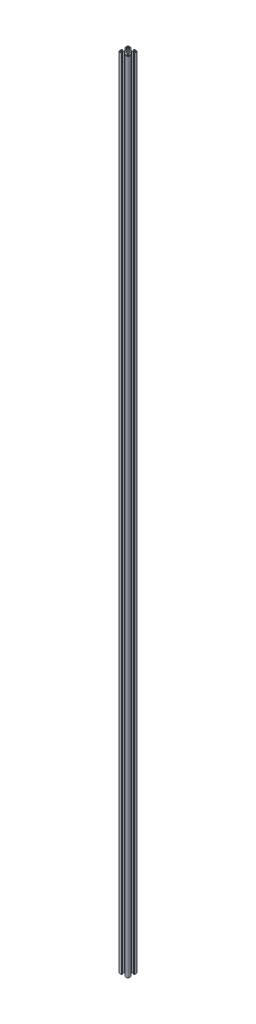
SolidWorks part; units mm, degrees
material "6063-T5"
ref_plane "前视基准面" through (0, 0, 0) normal (0, 0, 1) x (1, 0, 0)
ref_plane "上视基准面" through (0, 0, 0) normal (0, 1, 0) x (1, 0, 0)
ref_plane "右视基准面" through (0, 0, 0) normal (1, 0, 0) x (0, 0, -1)
sketch "草图3" plane through (0, 0, 0) normal (0, 1, 0) x (1, 0, 0)
  line L0 (0, 0) -> (-15, -15) construction
  line L1 (-15, -15) -> (-15, 0) construction
  line L2 (-15, 0) -> (0, 0) construction
  line L3 (-15, -12.5) -> (-15, -5.4)
  line L4 (-14.8, -5.2) -> (-14.4, -5.2)
  line L5 (-14.2, -5) -> (-14.2, -4.3)
  line L6 (-14, -4.1) -> (-13.2, -4.1)
  line L7 (-13.2, -4.1) -> (-13.2, -8.25)
  line L8 (-13.2, -8.25) -> (-9.5228, -8.25)
  line L9 (-9.5228, -8.25) -> (-5.8, -4.5272)
  line L10 (-5.8, -4.5272) -> (-5.8, 4.5272)
  line L11 (-13.2, -12.2) -> (-13.2, -11.05)
  line L12 (-12.2, -10.05) -> (-11.05, -10.05)
  line L13 (-4.5272, -5.8) -> (4.5272, -5.8)
  line L14 (-8.25, -9.5228) -> (-4.5272, -5.8)
  line L15 (-12.2, -13.2) -> (-11.05, -13.2)
  line L16 (-10.05, -12.2) -> (-10.05, -11.05)
  line L17 (-5.2, -14.8) -> (-5.2, -14.4)
  line L18 (-5, -14.2) -> (-4.3, -14.2)
  line L19 (-4.1, -14) -> (-4.1, -13.2)
  line L20 (-4.1, -13.2) -> (-8.25, -13.2)
  line L21 (-8.25, -13.2) -> (-8.25, -9.5228)
  line L22 (-12.5, -15) -> (-5.4, -15)
  line L23 (-12.5, 15) -> (-5.4, 15)
  line L24 (-8.25, 13.2) -> (-8.25, 9.5228)
  line L25 (-4.1, 13.2) -> (-8.25, 13.2)
  line L26 (-4.1, 14) -> (-4.1, 13.2)
  line L27 (-5, 14.2) -> (-4.3, 14.2)
  line L28 (-5.2, 14.8) -> (-5.2, 14.4)
  line L29 (-10.05, 12.2) -> (-10.05, 11.05)
  line L30 (-12.2, 13.2) -> (-11.05, 13.2)
  line L31 (-8.25, 9.5228) -> (-4.5272, 5.8)
  line L32 (-4.5272, 5.8) -> (4.5272, 5.8)
  line L33 (-12.2, 10.05) -> (-11.05, 10.05)
  line L34 (-13.2, 12.2) -> (-13.2, 11.05)
  line L35 (-9.5228, 8.25) -> (-5.8, 4.5272)
  line L36 (-13.2, 8.25) -> (-9.5228, 8.25)
  line L37 (-13.2, 4.1) -> (-13.2, 8.25)
  line L38 (-14, 4.1) -> (-13.2, 4.1)
  line L39 (-14.2, 5) -> (-14.2, 4.3)
  line L40 (-14.8, 5.2) -> (-14.4, 5.2)
  line L41 (-15, 12.5) -> (-15, 5.4)
  line L42 (0, 0) -> (0, -12.3268) construction
  line L43 (15, 12.5) -> (15, 5.4)
  line L44 (14.8, 5.2) -> (14.4, 5.2)
  line L45 (14.2, 5) -> (14.2, 4.3)
  line L46 (14, 4.1) -> (13.2, 4.1)
  line L47 (13.2, 4.1) -> (13.2, 8.25)
  line L48 (13.2, 8.25) -> (9.5228, 8.25)
  line L49 (9.5228, 8.25) -> (5.8, 4.5272)
  line L50 (13.2, 12.2) -> (13.2, 11.05)
  line L51 (12.2, 10.05) -> (11.05, 10.05)
  line L52 (8.25, 9.5228) -> (4.5272, 5.8)
  line L53 (12.2, 13.2) -> (11.05, 13.2)
  line L54 (10.05, 12.2) -> (10.05, 11.05)
  line L55 (5.2, 14.8) -> (5.2, 14.4)
  line L56 (5, 14.2) -> (4.3, 14.2)
  line L57 (4.1, 14) -> (4.1, 13.2)
  line L58 (4.1, 13.2) -> (8.25, 13.2)
  line L59 (8.25, 13.2) -> (8.25, 9.5228)
  line L60 (12.5, 15) -> (5.4, 15)
  line L61 (12.5, -15) -> (5.4, -15)
  line L62 (8.25, -13.2) -> (8.25, -9.5228)
  line L63 (4.1, -13.2) -> (8.25, -13.2)
  line L64 (4.1, -14) -> (4.1, -13.2)
  line L65 (5, -14.2) -> (4.3, -14.2)
  line L66 (5.2, -14.8) -> (5.2, -14.4)
  line L67 (10.05, -12.2) -> (10.05, -11.05)
  line L68 (12.2, -13.2) -> (11.05, -13.2)
  line L69 (8.25, -9.5228) -> (4.5272, -5.8)
  line L70 (12.2, -10.05) -> (11.05, -10.05)
  line L71 (13.2, -12.2) -> (13.2, -11.05)
  line L72 (5.8, -4.5272) -> (5.8, 4.5272)
  line L73 (9.5228, -8.25) -> (5.8, -4.5272)
  line L74 (13.2, -8.25) -> (9.5228, -8.25)
  line L75 (13.2, -4.1) -> (13.2, -8.25)
  line L76 (14, -4.1) -> (13.2, -4.1)
  line L77 (14.2, -5) -> (14.2, -4.3)
  line L78 (14.8, -5.2) -> (14.4, -5.2)
  line L79 (15, -12.5) -> (15, -5.4)
  circle A0 centre (0, 0) radius 3.4
  arc A1 (-12.5, 15) -> (-15, 12.5) centre (-12.5, 12.5) ccw
  arc A2 (15, 12.5) -> (12.5, 15) centre (12.5, 12.5) ccw
  arc A3 (12.5, -15) -> (15, -12.5) centre (12.5, -12.5) ccw
  arc A4 (-15, -12.5) -> (-12.5, -15) centre (-12.5, -12.5) ccw
  arc A5 (-12.2, 13.2) -> (-13.2, 12.2) centre (-12.2, 12.2) ccw
  arc A6 (-12.2, 10.05) -> (-13.2, 11.05) centre (-12.2, 11.05) cw
  arc A7 (-10.05, 11.05) -> (-11.05, 10.05) centre (-11.05, 11.05) cw
  arc A8 (-10.05, 12.2) -> (-11.05, 13.2) centre (-11.05, 12.2) ccw
  arc A9 (11.05, 10.05) -> (10.05, 11.05) centre (11.05, 11.05) cw
  arc A10 (11.05, 13.2) -> (10.05, 12.2) centre (11.05, 12.2) ccw
  arc A11 (13.2, 12.2) -> (12.2, 13.2) centre (12.2, 12.2) ccw
  arc A12 (13.2, 11.05) -> (12.2, 10.05) centre (12.2, 11.05) cw
  arc A13 (12.2, -10.05) -> (13.2, -11.05) centre (12.2, -11.05) cw
  arc A14 (10.05, -11.05) -> (11.05, -10.05) centre (11.05, -11.05) cw
  arc A15 (10.05, -12.2) -> (11.05, -13.2) centre (11.05, -12.2) ccw
  arc A16 (12.2, -13.2) -> (13.2, -12.2) centre (12.2, -12.2) ccw
  arc A17 (-13.2, -11.05) -> (-12.2, -10.05) centre (-12.2, -11.05) cw
  arc A18 (-11.05, -10.05) -> (-10.05, -11.05) centre (-11.05, -11.05) cw
  arc A19 (-11.05, -13.2) -> (-10.05, -12.2) centre (-11.05, -12.2) ccw
  arc A20 (-13.2, -12.2) -> (-12.2, -13.2) centre (-12.2, -12.2) ccw
  arc A21 (-15, -5.4) -> (-14.8, -5.2) centre (-14.8, -5.4) cw
  arc A22 (-14.4, -5.2) -> (-14.2, -5) centre (-14.4, -5) ccw
  arc A23 (-14.2, -4.3) -> (-14, -4.1) centre (-14, -4.3) cw
  arc A24 (-14, 4.1) -> (-14.2, 4.3) centre (-14, 4.3) cw
  arc A25 (-14.2, 5) -> (-14.4, 5.2) centre (-14.4, 5) ccw
  arc A26 (-14.8, 5.2) -> (-15, 5.4) centre (-14.8, 5.4) cw
  arc A27 (-5.4, 15) -> (-5.2, 14.8) centre (-5.4, 14.8) cw
  arc A28 (-5, 14.2) -> (-5.2, 14.4) centre (-5, 14.4) cw
  arc A29 (-4.1, 14) -> (-4.3, 14.2) centre (-4.3, 14) ccw
  arc A30 (5.2, 14.8) -> (5.4, 15) centre (5.4, 14.8) cw
  arc A31 (5.2, 14.4) -> (5, 14.2) centre (5, 14.4) cw
  arc A32 (4.3, 14.2) -> (4.1, 14) centre (4.3, 14) ccw
  arc A33 (15, 5.4) -> (14.8, 5.2) centre (14.8, 5.4) cw
  arc A34 (14.4, 5.2) -> (14.2, 5) centre (14.4, 5) ccw
  arc A35 (14.2, 4.3) -> (14, 4.1) centre (14, 4.3) cw
  arc A36 (14, -4.1) -> (14.2, -4.3) centre (14, -4.3) cw
  arc A37 (14.2, -5) -> (14.4, -5.2) centre (14.4, -5) ccw
  arc A38 (14.8, -5.2) -> (15, -5.4) centre (14.8, -5.4) cw
  arc A39 (5.4, -15) -> (5.2, -14.8) centre (5.4, -14.8) cw
  arc A40 (5, -14.2) -> (5.2, -14.4) centre (5, -14.4) cw
  arc A41 (4.1, -14) -> (4.3, -14.2) centre (4.3, -14) ccw
  arc A42 (-5.2, -14.4) -> (-5, -14.2) centre (-5, -14.4) cw
  arc A43 (-4.3, -14.2) -> (-4.1, -14) centre (-4.3, -14) ccw
  arc A44 (-5.2, -14.8) -> (-5.4, -15) centre (-5.4, -14.8) cw
  point P38 (-5.8, 0)
  point P46 (0, 5.8)
  point P47 (0, -5.8)
  point P83 (5.8, 0)
  point P87 (-15, 15)
  point P90 (15, 15)
  point P93 (15, -15)
  point P99 (-13.2, 13.2)
  point P102 (-13.2, 10.05)
  point P105 (-10.05, 10.05)
  point P108 (-10.05, 13.2)
  point P111 (10.05, 10.05)
  point P114 (10.05, 13.2)
  point P117 (13.2, 13.2)
  point P120 (13.2, 10.05)
  point P123 (13.2, -10.05)
  point P126 (10.05, -10.05)
  point P129 (10.05, -13.2)
  point P132 (13.2, -13.2)
  point P135 (-13.2, -10.05)
  point P138 (-10.05, -10.05)
  point P141 (-10.05, -13.2)
  point P144 (-13.2, -13.2)
  point P147 (-15, -5.2)
  point P150 (-14.2, -5.2)
  point P153 (-14.2, -4.1)
  point P156 (-14.2, 4.1)
  point P159 (-14.2, 5.2)
  point P162 (-15, 5.2)
  point P165 (-5.2, 15)
  point P168 (-5.2, 14.2)
  point P171 (-4.1, 14.2)
  point P174 (5.2, 15)
  point P177 (5.2, 14.2)
  point P180 (4.1, 14.2)
  point P183 (15, 5.2)
  point P186 (14.2, 5.2)
  point P189 (14.2, 4.1)
  point P192 (14.2, -4.1)
  point P195 (14.2, -5.2)
  point P198 (15, -5.2)
  point P201 (5.2, -15)
  point P204 (5.2, -14.2)
  point P207 (4.1, -14.2)
  point P210 (-5.2, -14.2)
  point P213 (-4.1, -14.2)
  point P216 (-5.2, -15)
  dimension "D11" = 6.8
  dimension "D12" = 2.5
  dimension "D13" = 1
  dimension "D14" = 0.2
  dimension "D2" = 15
  dimension "D3" = 4.1
  dimension "D4" = 5.2
  dimension "D5" = 0.8
  dimension "D6" = 1.8
  dimension "D7" = 9.2
  dimension "D8" = 8.25
  dimension "D9" = 0.9
  dimension "D10" = 1.8
extrude "凸台-拉伸1" add sketch "草图3" along normal blind 2477.2
